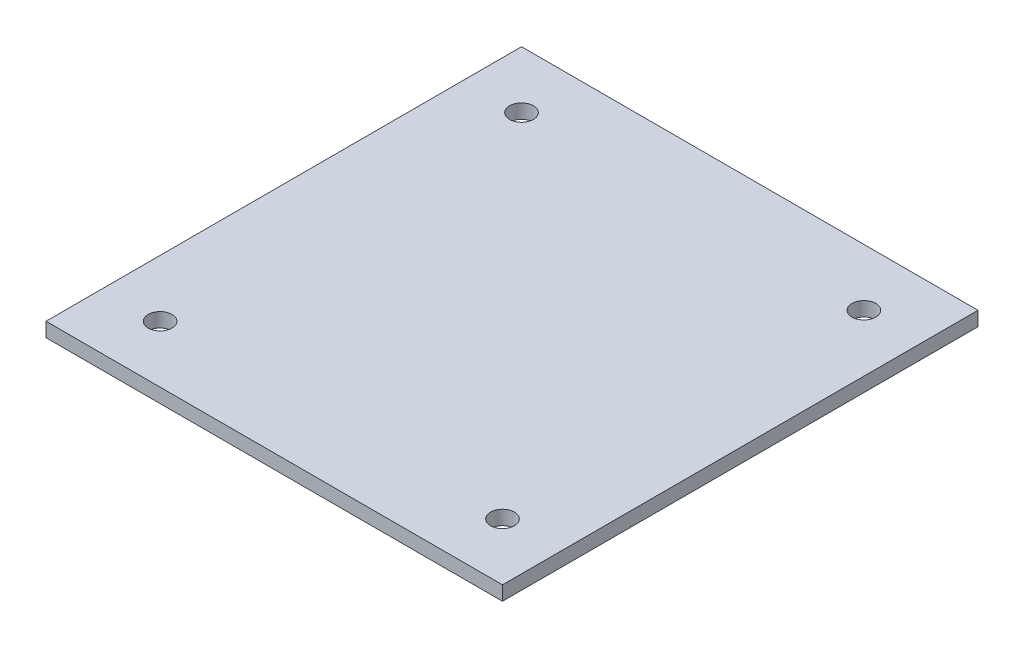
SolidWorks part; units mm, degrees
material "ASTM A36 Steel"
ref_plane "Front Plane" through (0, 0, 0) normal (0, 0, 1) x (1, 0, 0)
ref_plane "Top Plane" through (0, 0, 0) normal (0, 1, 0) x (1, 0, 0)
ref_plane "Right Plane" through (0, 0, 0) normal (1, 0, 0) x (0, 0, -1)
sketch "Sketch1" plane through (0, 0, 0) normal (0, 1, 0) x (1, 0, 0)
  line L1 (76.2, 79.375) -> (-76.2, 79.375)
  line L2 (76.2, 79.375) -> (76.2, -79.375)
  line L3 (76.2, -79.375) -> (-76.2, -79.375)
  line L4 (-76.2, 79.375) -> (-76.2, -79.375)
  line L5 (76.2, 79.375) -> (-76.2, -79.375) construction
  line L6 (76.2, -79.375) -> (-76.2, 79.375) construction
  point P0 (0, 0)
  dimension "D1" = 158.75
  dimension "D2" = 152.4
extrude "Boss-Extrude1" add sketch "Sketch1" along normal blind 4.7625
sketch "Sketch2" plane through (0, 4.7625, 0) normal (0, 1, 0) x (1, 0, 0)
  line L0 (-76.2, 79.375) -> (-76.2, -79.375) construction
  line L3 (57.15, -60.325) -> (-57.15, -60.325) construction
  line L6 (57.15, -60.325) -> (57.15, 60.325) construction
  line L7 (57.15, 60.325) -> (-57.15, 60.325) construction
  line L8 (-57.15, -60.325) -> (-57.15, 60.325) construction
  line L9 (57.15, -60.325) -> (-57.15, 60.325) construction
  line L10 (57.15, 60.325) -> (-57.15, -60.325) construction
  line L11 (-76.2, -79.375) -> (76.2, -79.375) construction
  line L12 (-57.15, -50.8) -> (-57.15, -69.85) construction
  line L13 (-53.975, -50.8) -> (-53.975, -69.85)
  line L14 (-60.325, -50.8) -> (-60.325, -69.85)
  line L15 (-57.15, 50.8) -> (-57.15, 69.85) construction
  line L16 (-60.325, 50.8) -> (-60.325, 69.85)
  line L17 (-53.975, 50.8) -> (-53.975, 69.85)
  line L18 (57.15, -50.8) -> (57.15, -69.85) construction
  line L19 (60.325, -50.8) -> (60.325, -69.85)
  line L20 (53.975, -50.8) -> (53.975, -69.85)
  line L21 (57.15, 69.85) -> (57.15, 50.8) construction
  line L22 (60.325, 69.85) -> (60.325, 50.8)
  line L23 (53.975, 69.85) -> (53.975, 50.8)
  arc A0 (-53.975, -50.8) -> (-60.325, -50.8) centre (-57.15, -50.8) ccw
  arc A1 (-60.325, -69.85) -> (-53.975, -69.85) centre (-57.15, -69.85) ccw
  arc A2 (-60.325, 50.8) -> (-53.975, 50.8) centre (-57.15, 50.8) ccw
  arc A3 (-53.975, 69.85) -> (-60.325, 69.85) centre (-57.15, 69.85) ccw
  arc A4 (60.325, -50.8) -> (53.975, -50.8) centre (57.15, -50.8) ccw
  arc A5 (53.975, -69.85) -> (60.325, -69.85) centre (57.15, -69.85) ccw
  arc A6 (60.325, 69.85) -> (53.975, 69.85) centre (57.15, 69.85) ccw
  arc A7 (53.975, 50.8) -> (60.325, 50.8) centre (57.15, 50.8) ccw
  point P0 (0, 0)
  point P11 (-57.15, -60.325)
  point P18 (-57.15, 60.325)
  point P27 (57.15, -60.325)
  point P34 (57.15, 60.325)
  dimension "D1" = 19.05
  dimension "D2" = 19.05
  dimension "D3" = 19.05
  dimension "D4" = 6.35
extrude "Cut-Extrude1" [suppressed] cut sketch "Sketch2" against normal through all
sketch "Sketch3" plane through (0, 4.7625, 0) normal (0, 1, 0) x (1, 0, 0)
  circle A0 centre (-57.15, 60.325) radius 3.9687
  circle A1 centre (57.15, 60.325) radius 3.9687
  circle A2 centre (-57.15, -60.325) radius 3.9687
  circle A3 centre (57.15, -60.325) radius 3.9687
  dimension "D1" = 7.9375
extrude "Cut-Extrude2" cut sketch "Sketch3" against normal through all
